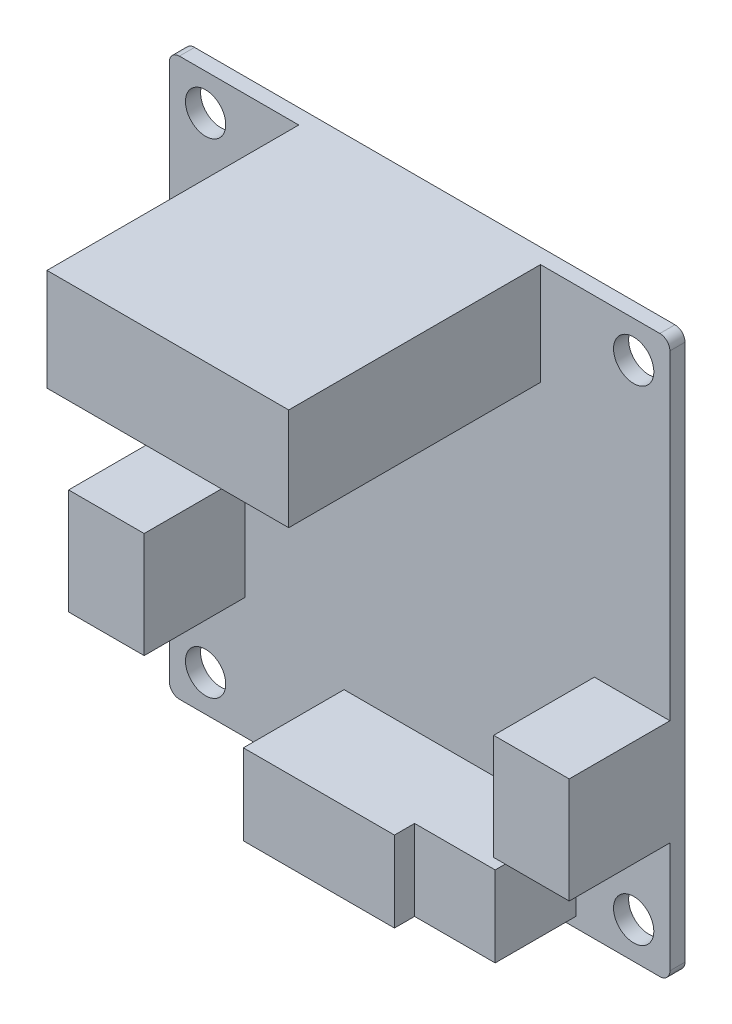
SolidWorks part; units mm, degrees
ref_plane "Plan de face" through (0, 0, 0) normal (0, 0, 1) x (1, 0, 0)
ref_plane "Plan de dessus" through (0, 0, 0) normal (0, 1, 0) x (1, 0, 0)
ref_plane "Plan de droite" through (0, 0, 0) normal (1, 0, 0) x (0, 0, -1)
sketch "Esquisse1" plane through (0, 0, 0) normal (0, 0, 1) x (1, 0, 0)
  line L0 (0, 27.65) -> (49.7, 27.65) construction
  line L1 (0, 0) -> (49.7, 0)
  line L2 (0, 0) -> (0, 55.3)
  line L3 (0, 55.3) -> (49.7, 55.3)
  line L4 (49.7, 0) -> (49.7, 55.3)
  line L5 (24.85, 55.3) -> (24.85, 0) construction
  circle A0 centre (3.6, 51.7) radius 2
  circle A1 centre (46.1, 51.7) radius 2
  circle A2 centre (46.1, 3.6) radius 2
  circle A3 centre (3.6, 3.6) radius 2
  dimension "D3" = 4
  dimension "D1" = 55.3
  dimension "D2" = 49.7
  dimension "D4" = 3.6
  dimension "D5" = 3.6
extrude "Boss.-Extru.1" add sketch "Esquisse1" along normal blind 1.5
fillet "Congé1" radius 1 4 edges at (0, 0, 0.75) (49.7, 0, 0.75) (49.7, 55.3, 0.75) (0, 55.3, 0.75)
sketch "Esquisse2" plane through (0, 0, 1.5) normal (0, 0, 1) x (1, 0, 0)
  line L0 (48.7, 55.3) -> (1, 55.3) construction
  line L1 (12.85, 45.1725) -> (36.85, 45.1725)
  line L2 (12.85, 45.1725) -> (12.85, 55.3)
  line L3 (12.85, 55.3) -> (36.85, 55.3)
  line L4 (36.85, 45.1725) -> (36.85, 55.3)
  line L5 (0, 54.3) -> (0, 1) construction
  dimension "D1" = 24
  dimension "D2" = 12.85
extrude "Boss.-Extru.2" add sketch "Esquisse2" along normal blind 25
sketch "Esquisse3" plane through (0, 0, 1.5) normal (0, 0, 1) x (1, 0, 0)
  line L0 (0, 54.3) -> (0, 1) construction
  line L1 (0, 12) -> (7.5, 12)
  line L2 (0, 12) -> (0, 22.5)
  line L3 (0, 22.5) -> (7.5, 22.5)
  line L4 (7.5, 12) -> (7.5, 22.5)
  line L5 (1, 0) -> (48.7, 0) construction
  line L6 (24.85, 0) -> (24.85, 33.2236) construction
  line L7 (42.2, 12) -> (42.2, 22.5)
  line L8 (49.7, 22.5) -> (42.2, 22.5)
  line L9 (49.7, 12) -> (49.7, 22.5)
  line L10 (49.7, 12) -> (42.2, 12)
  dimension "D1" = 10.5
  dimension "D2" = 7.5
  dimension "D3" = 12
extrude "Boss.-Extru.3" add sketch "Esquisse3" along normal blind 10
sketch "Esquisse4" plane through (0, 0, 1.5) normal (0, 0, 1) x (1, 0, 0)
  line L1 (17.35, 1) -> (32.35, 1)
  line L2 (17.35, 1) -> (17.35, 9)
  line L3 (17.35, 9) -> (32.35, 9)
  line L4 (32.35, 1) -> (32.35, 9)
  line L5 (49.7, 1) -> (49.7, 12) construction
  line L8 (1, 0) -> (48.7, 0) construction
  dimension "D1" = 15
  dimension "D2" = 8
  dimension "D3" = 17.35
  dimension "D4" = 9
extrude "Boss.-Extru.4" add sketch "Esquisse4" along normal blind 10
sketch "Esquisse5" plane through (0, 0, 1.5) normal (0, 0, 1) x (1, 0, 0)
  line L1 (32.35, 1) -> (40.35, 1)
  line L2 (32.35, 1) -> (32.35, 9)
  line L3 (32.35, 9) -> (40.35, 9)
  line L4 (40.35, 1) -> (40.35, 9)
  dimension "D1" = 8
  dimension "D2" = 8
extrude "Boss.-Extru.5" add sketch "Esquisse5" along normal blind 8
